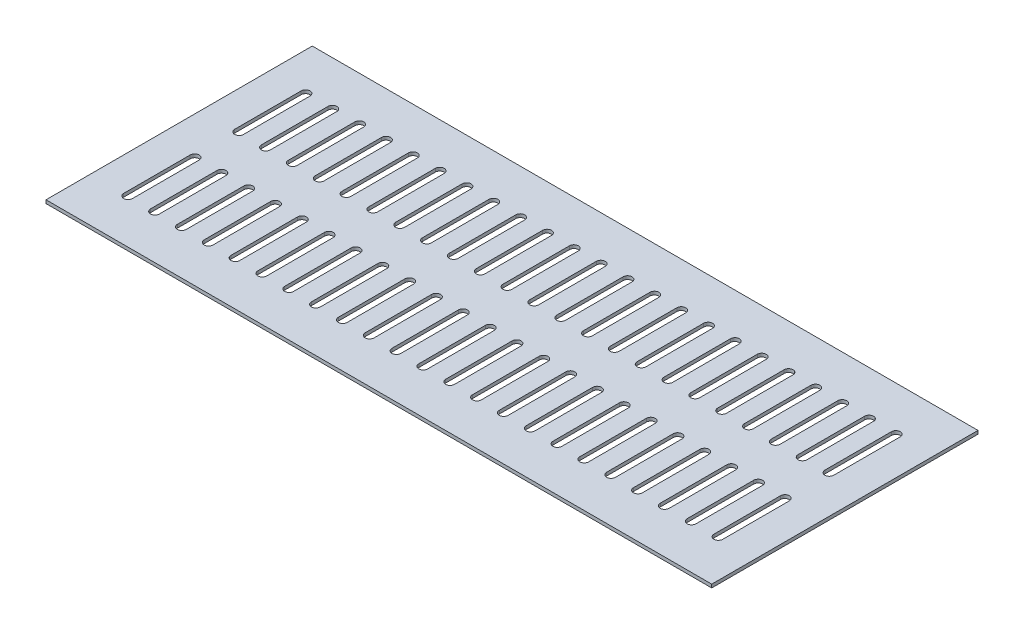
SolidWorks part; units mm, degrees
ref_plane "Ön Düzlem" through (0, 0, 0) normal (0, 0, 1) x (1, 0, 0)
ref_plane "Üst Düzlem" through (0, 0, 0) normal (0, 1, 0) x (1, 0, 0)
ref_plane "Sağ Düzlem" through (0, 0, 0) normal (1, 0, 0) x (0, 0, -1)
sketch "Çizim1" plane through (0, 0, 0) normal (0, 1, 0) x (1, 0, 0)
  line L0 (34, -40) -> (34, -100) construction
  line L1 (0, 0) -> (600, 0)
  line L2 (0, 0) -> (0, -240)
  line L3 (0, -240) -> (600, -240)
  line L4 (600, 0) -> (600, -240)
  line L5 (38, -40) -> (38, -100)
  line L6 (30, -40) -> (30, -100)
  line L7 (34, -140) -> (34, -200) construction
  line L8 (38, -140) -> (38, -200)
  line L9 (30, -140) -> (30, -200)
  line L10 (54.1818, -40) -> (54.1818, -100)
  line L11 (62.1818, -40) -> (62.1818, -100)
  line L12 (54.1818, -140) -> (54.1818, -200)
  line L13 (62.1818, -140) -> (62.1818, -200)
  line L14 (58.1818, -40) -> (58.1818, -100) construction
  line L15 (58.1818, -140) -> (58.1818, -200) construction
  line L16 (78.3636, -40) -> (78.3636, -100)
  line L17 (86.3636, -40) -> (86.3636, -100)
  line L18 (78.3636, -140) -> (78.3636, -200)
  line L19 (86.3636, -140) -> (86.3636, -200)
  line L20 (82.3636, -40) -> (82.3636, -100) construction
  line L21 (82.3636, -140) -> (82.3636, -200) construction
  line L22 (102.5455, -40) -> (102.5455, -100)
  line L23 (110.5455, -40) -> (110.5455, -100)
  line L24 (102.5455, -140) -> (102.5455, -200)
  line L25 (110.5455, -140) -> (110.5455, -200)
  line L26 (106.5455, -40) -> (106.5455, -100) construction
  line L27 (106.5455, -140) -> (106.5455, -200) construction
  line L28 (126.7273, -40) -> (126.7273, -100)
  line L29 (134.7273, -40) -> (134.7273, -100)
  line L30 (126.7273, -140) -> (126.7273, -200)
  line L31 (134.7273, -140) -> (134.7273, -200)
  line L32 (130.7273, -40) -> (130.7273, -100) construction
  line L33 (130.7273, -140) -> (130.7273, -200) construction
  line L34 (150.9091, -40) -> (150.9091, -100)
  line L35 (158.9091, -40) -> (158.9091, -100)
  line L36 (150.9091, -140) -> (150.9091, -200)
  line L37 (158.9091, -140) -> (158.9091, -200)
  line L38 (154.9091, -40) -> (154.9091, -100) construction
  line L39 (154.9091, -140) -> (154.9091, -200) construction
  line L40 (175.0909, -40) -> (175.0909, -100)
  line L41 (183.0909, -40) -> (183.0909, -100)
  line L42 (175.0909, -140) -> (175.0909, -200)
  line L43 (183.0909, -140) -> (183.0909, -200)
  line L44 (179.0909, -40) -> (179.0909, -100) construction
  line L45 (179.0909, -140) -> (179.0909, -200) construction
  line L46 (199.2727, -40) -> (199.2727, -100)
  line L47 (207.2727, -40) -> (207.2727, -100)
  line L48 (199.2727, -140) -> (199.2727, -200)
  line L49 (207.2727, -140) -> (207.2727, -200)
  line L50 (203.2727, -40) -> (203.2727, -100) construction
  line L51 (203.2727, -140) -> (203.2727, -200) construction
  line L52 (223.4545, -40) -> (223.4545, -100)
  line L53 (231.4545, -40) -> (231.4545, -100)
  line L54 (223.4545, -140) -> (223.4545, -200)
  line L55 (231.4545, -140) -> (231.4545, -200)
  line L56 (227.4545, -40) -> (227.4545, -100) construction
  line L57 (227.4545, -140) -> (227.4545, -200) construction
  line L58 (247.6364, -40) -> (247.6364, -100)
  line L59 (255.6364, -40) -> (255.6364, -100)
  line L60 (247.6364, -140) -> (247.6364, -200)
  line L61 (255.6364, -140) -> (255.6364, -200)
  line L62 (251.6364, -40) -> (251.6364, -100) construction
  line L63 (251.6364, -140) -> (251.6364, -200) construction
  line L64 (271.8182, -40) -> (271.8182, -100)
  line L65 (279.8182, -40) -> (279.8182, -100)
  line L66 (271.8182, -140) -> (271.8182, -200)
  line L67 (279.8182, -140) -> (279.8182, -200)
  line L68 (275.8182, -40) -> (275.8182, -100) construction
  line L69 (275.8182, -140) -> (275.8182, -200) construction
  line L70 (296, -40) -> (296, -100)
  line L71 (304, -40) -> (304, -100)
  line L72 (296, -140) -> (296, -200)
  line L73 (304, -140) -> (304, -200)
  line L74 (300, -40) -> (300, -100) construction
  line L75 (300, -140) -> (300, -200) construction
  line L76 (320.1818, -40) -> (320.1818, -100)
  line L77 (328.1818, -40) -> (328.1818, -100)
  line L78 (320.1818, -140) -> (320.1818, -200)
  line L79 (328.1818, -140) -> (328.1818, -200)
  line L80 (324.1818, -40) -> (324.1818, -100) construction
  line L81 (324.1818, -140) -> (324.1818, -200) construction
  line L82 (344.3636, -40) -> (344.3636, -100)
  line L83 (352.3636, -40) -> (352.3636, -100)
  line L84 (344.3636, -140) -> (344.3636, -200)
  line L85 (352.3636, -140) -> (352.3636, -200)
  line L86 (348.3636, -40) -> (348.3636, -100) construction
  line L87 (348.3636, -140) -> (348.3636, -200) construction
  line L88 (368.5455, -40) -> (368.5455, -100)
  line L89 (376.5455, -40) -> (376.5455, -100)
  line L90 (368.5455, -140) -> (368.5455, -200)
  line L91 (376.5455, -140) -> (376.5455, -200)
  line L92 (372.5455, -40) -> (372.5455, -100) construction
  line L93 (372.5455, -140) -> (372.5455, -200) construction
  line L94 (392.7273, -40) -> (392.7273, -100)
  line L95 (400.7273, -40) -> (400.7273, -100)
  line L96 (392.7273, -140) -> (392.7273, -200)
  line L97 (400.7273, -140) -> (400.7273, -200)
  line L98 (396.7273, -40) -> (396.7273, -100) construction
  line L99 (396.7273, -140) -> (396.7273, -200) construction
  line L100 (416.9091, -40) -> (416.9091, -100)
  line L101 (424.9091, -40) -> (424.9091, -100)
  line L102 (416.9091, -140) -> (416.9091, -200)
  line L103 (424.9091, -140) -> (424.9091, -200)
  line L104 (420.9091, -40) -> (420.9091, -100) construction
  line L105 (420.9091, -140) -> (420.9091, -200) construction
  line L106 (441.0909, -40) -> (441.0909, -100)
  line L107 (449.0909, -40) -> (449.0909, -100)
  line L108 (441.0909, -140) -> (441.0909, -200)
  line L109 (449.0909, -140) -> (449.0909, -200)
  line L110 (445.0909, -40) -> (445.0909, -100) construction
  line L111 (445.0909, -140) -> (445.0909, -200) construction
  line L112 (465.2727, -40) -> (465.2727, -100)
  line L113 (473.2727, -40) -> (473.2727, -100)
  line L114 (465.2727, -140) -> (465.2727, -200)
  line L115 (473.2727, -140) -> (473.2727, -200)
  line L116 (469.2727, -40) -> (469.2727, -100) construction
  line L117 (469.2727, -140) -> (469.2727, -200) construction
  line L118 (489.4545, -40) -> (489.4545, -100)
  line L119 (497.4545, -40) -> (497.4545, -100)
  line L120 (489.4545, -140) -> (489.4545, -200)
  line L121 (497.4545, -140) -> (497.4545, -200)
  line L122 (493.4545, -40) -> (493.4545, -100) construction
  line L123 (493.4545, -140) -> (493.4545, -200) construction
  line L124 (513.6364, -40) -> (513.6364, -100)
  line L125 (521.6364, -40) -> (521.6364, -100)
  line L126 (513.6364, -140) -> (513.6364, -200)
  line L127 (521.6364, -140) -> (521.6364, -200)
  line L128 (517.6364, -40) -> (517.6364, -100) construction
  line L129 (517.6364, -140) -> (517.6364, -200) construction
  line L130 (537.8182, -40) -> (537.8182, -100)
  line L131 (545.8182, -40) -> (545.8182, -100)
  line L132 (537.8182, -140) -> (537.8182, -200)
  line L133 (545.8182, -140) -> (545.8182, -200)
  line L134 (541.8182, -40) -> (541.8182, -100) construction
  line L135 (541.8182, -140) -> (541.8182, -200) construction
  line L136 (562, -40) -> (562, -100)
  line L137 (570, -40) -> (570, -100)
  line L138 (562, -140) -> (562, -200)
  line L139 (570, -140) -> (570, -200)
  line L140 (566, -40) -> (566, -100) construction
  line L141 (566, -140) -> (566, -200) construction
  arc A0 (38, -40) -> (30, -40) centre (34, -40) ccw
  arc A1 (30, -100) -> (38, -100) centre (34, -100) ccw
  arc A2 (38, -140) -> (30, -140) centre (34, -140) ccw
  arc A3 (30, -200) -> (38, -200) centre (34, -200) ccw
  arc A4 (62.1818, -40) -> (54.1818, -40) centre (58.1818, -40) ccw
  arc A5 (54.1818, -100) -> (62.1818, -100) centre (58.1818, -100) ccw
  arc A6 (62.1818, -140) -> (54.1818, -140) centre (58.1818, -140) ccw
  arc A7 (54.1818, -200) -> (62.1818, -200) centre (58.1818, -200) ccw
  arc A8 (86.3636, -40) -> (78.3636, -40) centre (82.3636, -40) ccw
  arc A9 (78.3636, -100) -> (86.3636, -100) centre (82.3636, -100) ccw
  arc A10 (86.3636, -140) -> (78.3636, -140) centre (82.3636, -140) ccw
  arc A11 (78.3636, -200) -> (86.3636, -200) centre (82.3636, -200) ccw
  arc A12 (110.5455, -40) -> (102.5455, -40) centre (106.5455, -40) ccw
  arc A13 (102.5455, -100) -> (110.5455, -100) centre (106.5455, -100) ccw
  arc A14 (110.5455, -140) -> (102.5455, -140) centre (106.5455, -140) ccw
  arc A15 (102.5455, -200) -> (110.5455, -200) centre (106.5455, -200) ccw
  arc A16 (134.7273, -40) -> (126.7273, -40) centre (130.7273, -40) ccw
  arc A17 (126.7273, -100) -> (134.7273, -100) centre (130.7273, -100) ccw
  arc A18 (134.7273, -140) -> (126.7273, -140) centre (130.7273, -140) ccw
  arc A19 (126.7273, -200) -> (134.7273, -200) centre (130.7273, -200) ccw
  arc A20 (158.9091, -40) -> (150.9091, -40) centre (154.9091, -40) ccw
  arc A21 (150.9091, -100) -> (158.9091, -100) centre (154.9091, -100) ccw
  arc A22 (158.9091, -140) -> (150.9091, -140) centre (154.9091, -140) ccw
  arc A23 (150.9091, -200) -> (158.9091, -200) centre (154.9091, -200) ccw
  arc A24 (183.0909, -40) -> (175.0909, -40) centre (179.0909, -40) ccw
  arc A25 (175.0909, -100) -> (183.0909, -100) centre (179.0909, -100) ccw
  arc A26 (183.0909, -140) -> (175.0909, -140) centre (179.0909, -140) ccw
  arc A27 (175.0909, -200) -> (183.0909, -200) centre (179.0909, -200) ccw
  arc A28 (207.2727, -40) -> (199.2727, -40) centre (203.2727, -40) ccw
  arc A29 (199.2727, -100) -> (207.2727, -100) centre (203.2727, -100) ccw
  arc A30 (207.2727, -140) -> (199.2727, -140) centre (203.2727, -140) ccw
  arc A31 (199.2727, -200) -> (207.2727, -200) centre (203.2727, -200) ccw
  arc A32 (231.4545, -40) -> (223.4545, -40) centre (227.4545, -40) ccw
  arc A33 (223.4545, -100) -> (231.4545, -100) centre (227.4545, -100) ccw
  arc A34 (231.4545, -140) -> (223.4545, -140) centre (227.4545, -140) ccw
  arc A35 (223.4545, -200) -> (231.4545, -200) centre (227.4545, -200) ccw
  arc A36 (255.6364, -40) -> (247.6364, -40) centre (251.6364, -40) ccw
  arc A37 (247.6364, -100) -> (255.6364, -100) centre (251.6364, -100) ccw
  arc A38 (255.6364, -140) -> (247.6364, -140) centre (251.6364, -140) ccw
  arc A39 (247.6364, -200) -> (255.6364, -200) centre (251.6364, -200) ccw
  arc A40 (279.8182, -40) -> (271.8182, -40) centre (275.8182, -40) ccw
  arc A41 (271.8182, -100) -> (279.8182, -100) centre (275.8182, -100) ccw
  arc A42 (279.8182, -140) -> (271.8182, -140) centre (275.8182, -140) ccw
  arc A43 (271.8182, -200) -> (279.8182, -200) centre (275.8182, -200) ccw
  arc A44 (304, -40) -> (296, -40) centre (300, -40) ccw
  arc A45 (296, -100) -> (304, -100) centre (300, -100) ccw
  arc A46 (304, -140) -> (296, -140) centre (300, -140) ccw
  arc A47 (296, -200) -> (304, -200) centre (300, -200) ccw
  arc A48 (328.1818, -40) -> (320.1818, -40) centre (324.1818, -40) ccw
  arc A49 (320.1818, -100) -> (328.1818, -100) centre (324.1818, -100) ccw
  arc A50 (328.1818, -140) -> (320.1818, -140) centre (324.1818, -140) ccw
  arc A51 (320.1818, -200) -> (328.1818, -200) centre (324.1818, -200) ccw
  arc A52 (352.3636, -40) -> (344.3636, -40) centre (348.3636, -40) ccw
  arc A53 (344.3636, -100) -> (352.3636, -100) centre (348.3636, -100) ccw
  arc A54 (352.3636, -140) -> (344.3636, -140) centre (348.3636, -140) ccw
  arc A55 (344.3636, -200) -> (352.3636, -200) centre (348.3636, -200) ccw
  arc A56 (376.5455, -40) -> (368.5455, -40) centre (372.5455, -40) ccw
  arc A57 (368.5455, -100) -> (376.5455, -100) centre (372.5455, -100) ccw
  arc A58 (376.5455, -140) -> (368.5455, -140) centre (372.5455, -140) ccw
  arc A59 (368.5455, -200) -> (376.5455, -200) centre (372.5455, -200) ccw
  arc A60 (400.7273, -40) -> (392.7273, -40) centre (396.7273, -40) ccw
  arc A61 (392.7273, -100) -> (400.7273, -100) centre (396.7273, -100) ccw
  arc A62 (400.7273, -140) -> (392.7273, -140) centre (396.7273, -140) ccw
  arc A63 (392.7273, -200) -> (400.7273, -200) centre (396.7273, -200) ccw
  arc A64 (424.9091, -40) -> (416.9091, -40) centre (420.9091, -40) ccw
  arc A65 (416.9091, -100) -> (424.9091, -100) centre (420.9091, -100) ccw
  arc A66 (424.9091, -140) -> (416.9091, -140) centre (420.9091, -140) ccw
  arc A67 (416.9091, -200) -> (424.9091, -200) centre (420.9091, -200) ccw
  arc A68 (449.0909, -40) -> (441.0909, -40) centre (445.0909, -40) ccw
  arc A69 (441.0909, -100) -> (449.0909, -100) centre (445.0909, -100) ccw
  arc A70 (449.0909, -140) -> (441.0909, -140) centre (445.0909, -140) ccw
  arc A71 (441.0909, -200) -> (449.0909, -200) centre (445.0909, -200) ccw
  arc A72 (473.2727, -40) -> (465.2727, -40) centre (469.2727, -40) ccw
  arc A73 (465.2727, -100) -> (473.2727, -100) centre (469.2727, -100) ccw
  arc A74 (473.2727, -140) -> (465.2727, -140) centre (469.2727, -140) ccw
  arc A75 (465.2727, -200) -> (473.2727, -200) centre (469.2727, -200) ccw
  arc A76 (497.4545, -40) -> (489.4545, -40) centre (493.4545, -40) ccw
  arc A77 (489.4545, -100) -> (497.4545, -100) centre (493.4545, -100) ccw
  arc A78 (497.4545, -140) -> (489.4545, -140) centre (493.4545, -140) ccw
  arc A79 (489.4545, -200) -> (497.4545, -200) centre (493.4545, -200) ccw
  arc A80 (521.6364, -40) -> (513.6364, -40) centre (517.6364, -40) ccw
  arc A81 (513.6364, -100) -> (521.6364, -100) centre (517.6364, -100) ccw
  arc A82 (521.6364, -140) -> (513.6364, -140) centre (517.6364, -140) ccw
  arc A83 (513.6364, -200) -> (521.6364, -200) centre (517.6364, -200) ccw
  arc A84 (545.8182, -40) -> (537.8182, -40) centre (541.8182, -40) ccw
  arc A85 (537.8182, -100) -> (545.8182, -100) centre (541.8182, -100) ccw
  arc A86 (545.8182, -140) -> (537.8182, -140) centre (541.8182, -140) ccw
  arc A87 (537.8182, -200) -> (545.8182, -200) centre (541.8182, -200) ccw
  arc A88 (570, -40) -> (562, -40) centre (566, -40) ccw
  arc A89 (562, -100) -> (570, -100) centre (566, -100) ccw
  arc A90 (570, -140) -> (562, -140) centre (566, -140) ccw
  arc A91 (562, -200) -> (570, -200) centre (566, -200) ccw
  point P7 (34, -70)
  point P12 (34, -170)
  point P22 (58.1818, -70)
  point P27 (58.1818, -170)
  point P36 (82.3636, -70)
  point P41 (82.3636, -170)
  point P50 (106.5455, -70)
  point P55 (106.5455, -170)
  point P64 (130.7273, -70)
  point P69 (130.7273, -170)
  point P78 (154.9091, -70)
  point P83 (154.9091, -170)
  point P92 (179.0909, -70)
  point P97 (179.0909, -170)
  point P106 (203.2727, -70)
  point P111 (203.2727, -170)
  point P120 (227.4545, -70)
  point P125 (227.4545, -170)
  point P134 (251.6364, -70)
  point P139 (251.6364, -170)
  point P148 (275.8182, -70)
  point P153 (275.8182, -170)
  point P162 (300, -70)
  point P167 (300, -170)
  point P176 (324.1818, -70)
  point P181 (324.1818, -170)
  point P190 (348.3636, -70)
  point P195 (348.3636, -170)
  point P204 (372.5455, -70)
  point P209 (372.5455, -170)
  point P218 (396.7273, -70)
  point P223 (396.7273, -170)
  point P232 (420.9091, -70)
  point P237 (420.9091, -170)
  point P246 (445.0909, -70)
  point P251 (445.0909, -170)
  point P260 (469.2727, -70)
  point P265 (469.2727, -170)
  point P274 (493.4545, -70)
  point P279 (493.4545, -170)
  point P288 (517.6364, -70)
  point P293 (517.6364, -170)
  point P302 (541.8182, -70)
  point P307 (541.8182, -170)
  point P316 (566, -70)
  point P321 (566, -170)
  dimension "D6" = 40
  dimension "D7" = 40
  dimension "D1" = 600
  dimension "D2" = 240
  dimension "D3" = 8
  dimension "D4" = 60
  dimension "D5" = 30
  dimension "D9" = 30
  dimension "D8" = 23
extrude "Yükseklik-Ekstrüzyon1" add sketch "Çizim1" along normal blind 3
